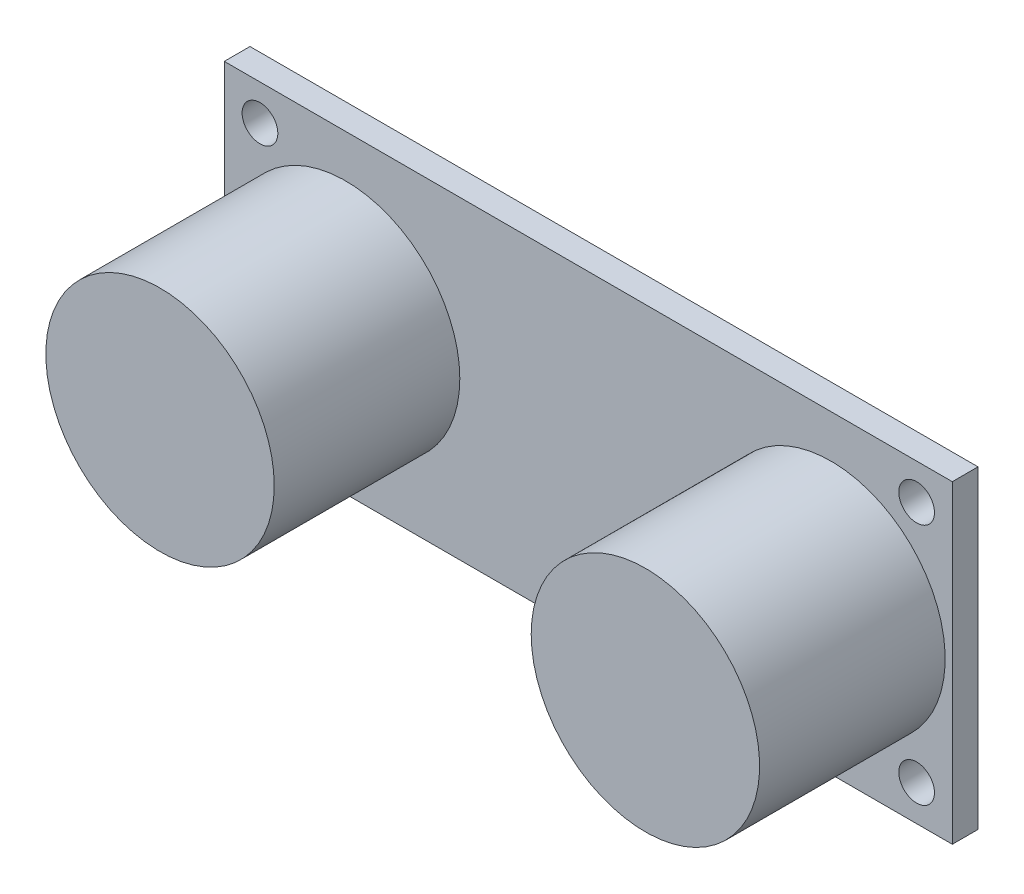
SolidWorks part; units mm, degrees
ref_plane "Ön Düzlem" through (0, 0, 0) normal (0, 0, 1) x (1, 0, 0)
ref_plane "Üst Düzlem" through (0, 0, 0) normal (0, 1, 0) x (1, 0, 0)
ref_plane "Sağ Düzlem" through (0, 0, 0) normal (1, 0, 0) x (0, 0, -1)
sketch "Sketch1" plane through (0, 0, 0) normal (0, 0, 1) x (1, 0, 0)
  line L0 (0, 0) -> (-35.6773, 0) construction
  line L1 (-25.5, 11) -> (25.5, 11)
  line L2 (-25.5, 11) -> (-25.5, -11)
  line L3 (-25.5, -11) -> (25.5, -11)
  line L4 (25.5, 11) -> (25.5, -11)
  line L5 (-25.5, 11) -> (25.5, -11) construction
  line L6 (-25.5, -11) -> (25.5, 11) construction
  line L7 (0, 0) -> (31.1473, 0) construction
  line L8 (0, 0) -> (0, 12.7926) construction
  line L9 (0, 0) -> (0, -13.5182) construction
  circle A0 centre (-23, -8.5) radius 1.25
  circle A1 centre (-23, 8.5) radius 1.25
  circle A2 centre (23, 8.5) radius 1.25
  circle A3 centre (23, -8.5) radius 1.25
  point P0 (0, 0)
  point P19 (0, 0)
  point P21 (23.676, 8.8734)
  dimension "D3" = 17
  dimension "D4" = 46
  dimension "D1" = 22
  dimension "D2" = 51
extrude "Boss-Extrude1" add sketch "Sketch1" along normal blind 1.8
sketch "Sketch2" plane through (0, 0, 1.8) normal (0, 0, 1) x (1, 0, 0)
  line L2 (35.5942, 0) -> (-35.5942, 0) construction
  line L3 (17, 0) -> (17, -15.7417) construction
  line L4 (-17, 0) -> (-17, 13.586) construction
  line L5 (-17, 0) -> (-17, -15.7417) construction
  line L6 (17, 0) -> (17, 13.586) construction
  circle A0 centre (-17, 0) radius 8
  circle A1 centre (17, 0) radius 8
extrude "Boss-Extrude2" add sketch "Sketch2" along normal blind 13
